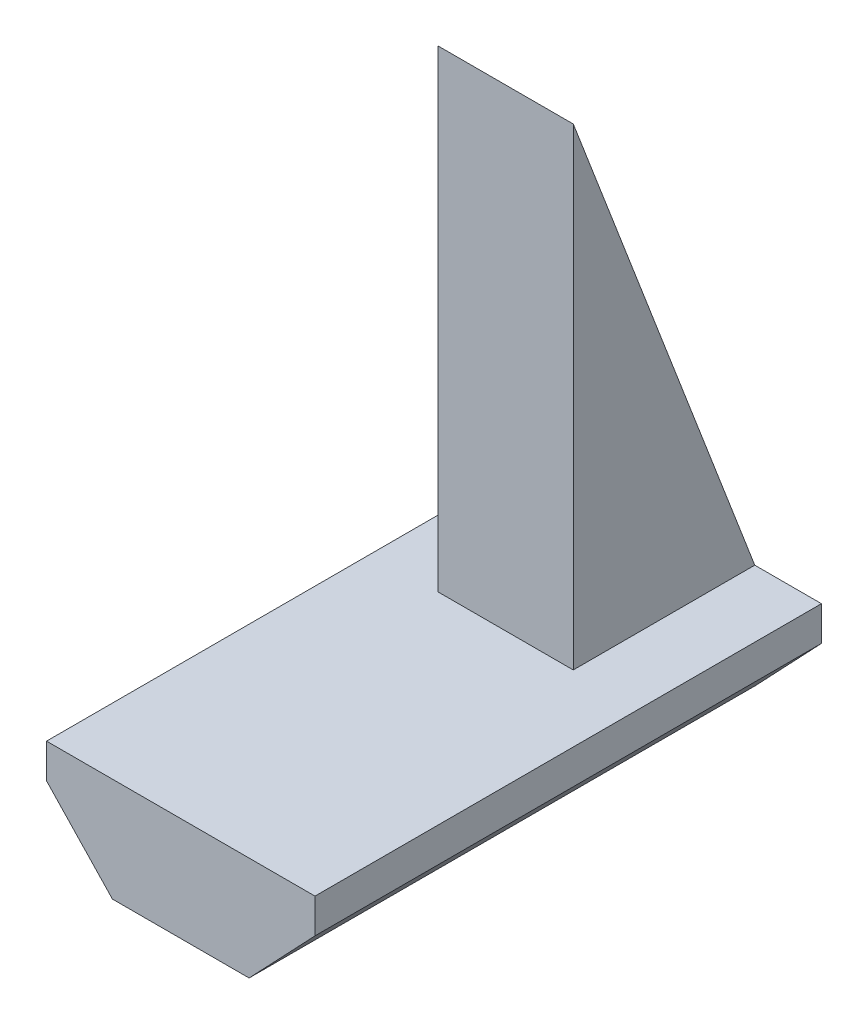
SolidWorks part; units mm, degrees
ref_plane "Front Plane" through (0, 0, 0) normal (0, 0, 1) x (1, 0, 0)
ref_plane "Top Plane" through (0, 0, 0) normal (0, 1, 0) x (1, 0, 0)
ref_plane "Right Plane" through (0, 0, 0) normal (1, 0, 0) x (0, 0, -1)
sketch "Sketch1" plane through (0, 0, 0) normal (0, 0, 1) x (1, 0, 0)
  line L7 (0, 0) -> (0, 9.9098) construction
  line B0 (7.95, 0) -> (7.95, -2.04)
  line B1 (4.048, -6.1524) -> (-4.048, -6.1524)
  line B2 (-7.95, -2.04) -> (-7.95, 0)
  line B3 (-7.95, 0) -> (7.95, 0)
  line B4 (7.95, -2.04) -> (4.048, -6.1524)
  line B5 (-4.048, -6.1524) -> (-7.95, -2.04)
  line B6 (4.05, 0) -> (-4.05, 0) construction
sketch_block_instance "Extrusion Profile-2"
sketch_block "Extrusion Profile" parameters "D1"=8.44, "D2"=2.6, "D3"=6, "D4"=16.7, "D6"=5.6686, "D7"=2.0404, "D8"=8.0963, "D9"=15.9, "D5"=2.4157
extrude "Boss-Extrude1" add sketch "Sketch1" along normal blind 30 contours B2 B5 B1 B4 B0 B3
ref_plane "Plane1" through (0, 0, 0) normal (-1, 0, 0) x (0, 0, 1)
sketch "Sketch2" plane through (0, 0, 0) normal (-1, 0, 0) x (0, 0, 1)
  line L0 (0, 0) -> (10.751, 28.0074)
  line L1 (10.751, 28.0074) -> (10.751, 0)
  line L2 (30, 0) -> (0, 0) construction
  line L3 (10.751, 0) -> (0, 0)
  dimension "D1" = 69
  dimension "D2" = 30
extrude "Boss-Extrude3" add sketch "Sketch2" along normal mid plane 8
